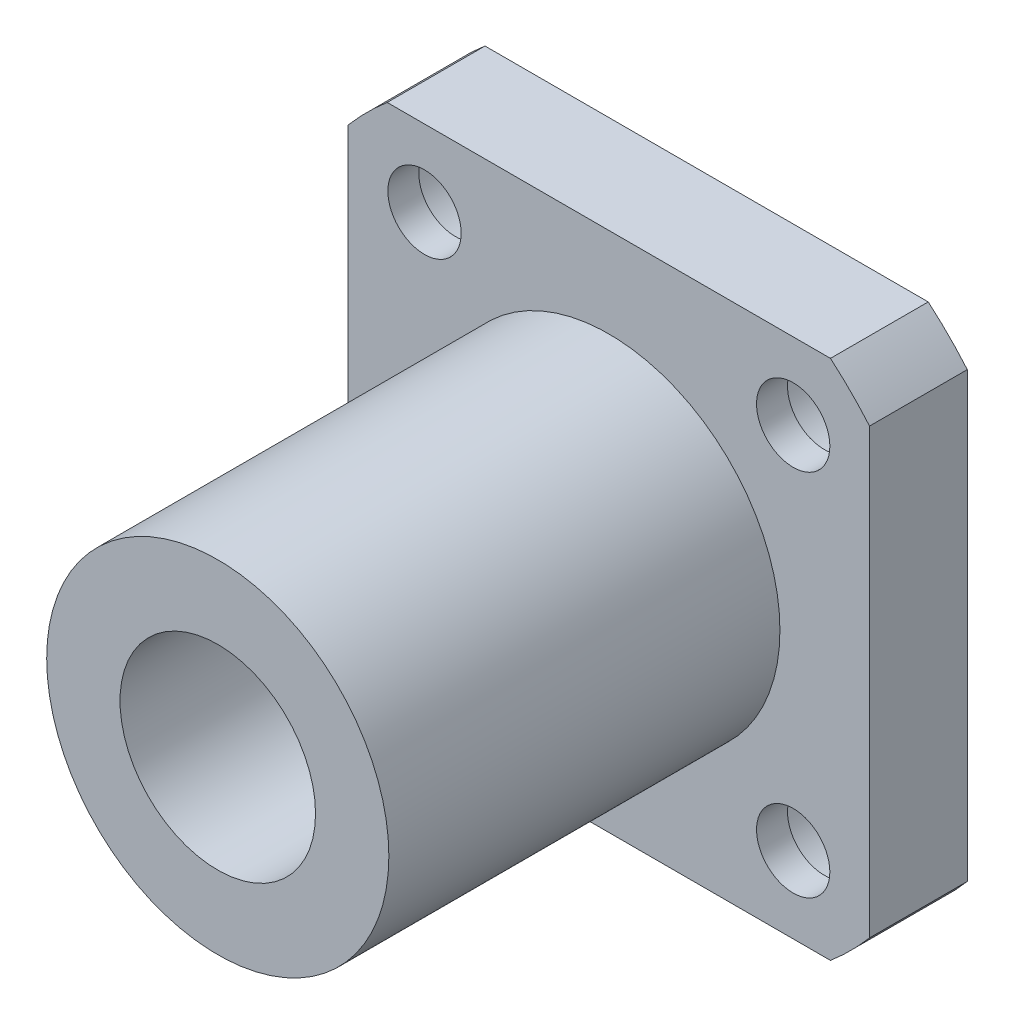
SolidWorks part; units mm, degrees
ref_plane "前视基准面" through (0, 0, 0) normal (0, 0, 1) x (1, 0, 0)
ref_plane "上视基准面" through (0, 0, 0) normal (0, 1, 0) x (1, 0, 0)
ref_plane "右视基准面" through (0, 0, 0) normal (1, 0, 0) x (0, 0, -1)
sketch "草图1" plane through (0, 0, 0) normal (0, 0, 1) x (1, 0, 0)
  line L1 (-13.6015, 16) -> (13.6015, 16)
  line L2 (-16, 13.6015) -> (-16, -13.6015)
  line L3 (-13.6015, -16) -> (13.6015, -16)
  line L4 (16, 13.6015) -> (16, -13.6015)
  arc A0 (-13.6015, 16) -> (-16, 13.6015) centre (0, 0) ccw
  arc A1 (16, 13.6015) -> (13.6015, 16) centre (0, 0) ccw
  arc A2 (13.6015, -16) -> (16, -13.6015) centre (0, 0) ccw
  arc A3 (-16, -13.6015) -> (-13.6015, -16) centre (0, 0) ccw
  dimension "D5" = 42
  dimension "D3" = 16
  dimension "D4" = 16
extrude "凸台-拉伸1" add sketch "草图1" along normal blind 6
sketch "草图2" plane through (0, 0, 6) normal (0, 0, 1) x (1, 0, 0)
  circle A0 centre (0, 0) radius 10.5
  dimension "D1" = 21
extrude "凸台-拉伸2" add sketch "草图2" along normal blind 24
sketch "草图3" plane through (0, 0, 30) normal (0, 0, 1) x (1, 0, 0)
  circle A0 centre (0, 0) radius 6
  dimension "D1" = 12
extrude "切除-拉伸1" cut sketch "草图3" against normal blind 30
sketch "草图4" plane through (0, 0, 6) normal (0, 0, 1) x (1, 0, 0)
  line L0 (0, 0) -> (-14.8492, 14.8492)
  line L1 (-14.8492, 14.8492) -> (14.8492, -14.8492)
  line L2 (0, 0) -> (-14.8492, -14.8492)
  line L3 (-14.8492, -14.8492) -> (14.8492, 14.8492)
  circle A0 centre (0, 0) radius 16
  arc A1 (-13.6015, 16) -> (-16, 13.6015) centre (0, 0) ccw construction
  arc A2 (13.6015, -16) -> (16, -13.6015) centre (0, 0) ccw construction
  arc A3 (-16, -13.6015) -> (-13.6015, -16) centre (0, 0) ccw construction
  arc A4 (16, 13.6015) -> (13.6015, 16) centre (0, 0) ccw construction
  circle A5 centre (11.3137, 11.3137) radius 2.25
  circle A6 centre (-11.3137, 11.3137) radius 2.25
  circle A7 centre (-11.3137, -11.3137) radius 2.25
  circle A8 centre (11.3137, -11.3137) radius 2.25
  dimension "D1" = 4.5
  dimension "D2" = 4.5
  dimension "D3" = 4.5
  dimension "D4" = 4.5
extrude "切除-拉伸2" cut sketch "草图4" against normal blind 1.9 contours A0 A6 L1 | L1 A6 A0 | A0 A6 L1 | L1 A6 A0 | L3 A5 A0 | A0 A5 L3 | L3 A5 A0 | A0 A5 L3 | A0 A8 L1 | L1 A8 A0 | A0 A8 L1 | L1 A8 A0 | L3 A7 A0 | A0 A7 L3 | L3 A7 A0 | A0 A7 L3
sketch "草图5" plane through (0, 0, 4.1) normal (0, 0, 1) x (1, 0, 0)
  circle A0 centre (-11.3137, 11.3137) radius 3.75
  circle A1 centre (11.3137, 11.3137) radius 3.75
  circle A2 centre (11.3137, -11.3137) radius 3.75
  circle A3 centre (-11.3137, -11.3137) radius 3.75
  dimension "D1" = 7.5
  dimension "D2" = 7.5
  dimension "D3" = 7.5
  dimension "D4" = 7.5
extrude "切除-拉伸3" cut sketch "草图5" against normal blind 4.1
